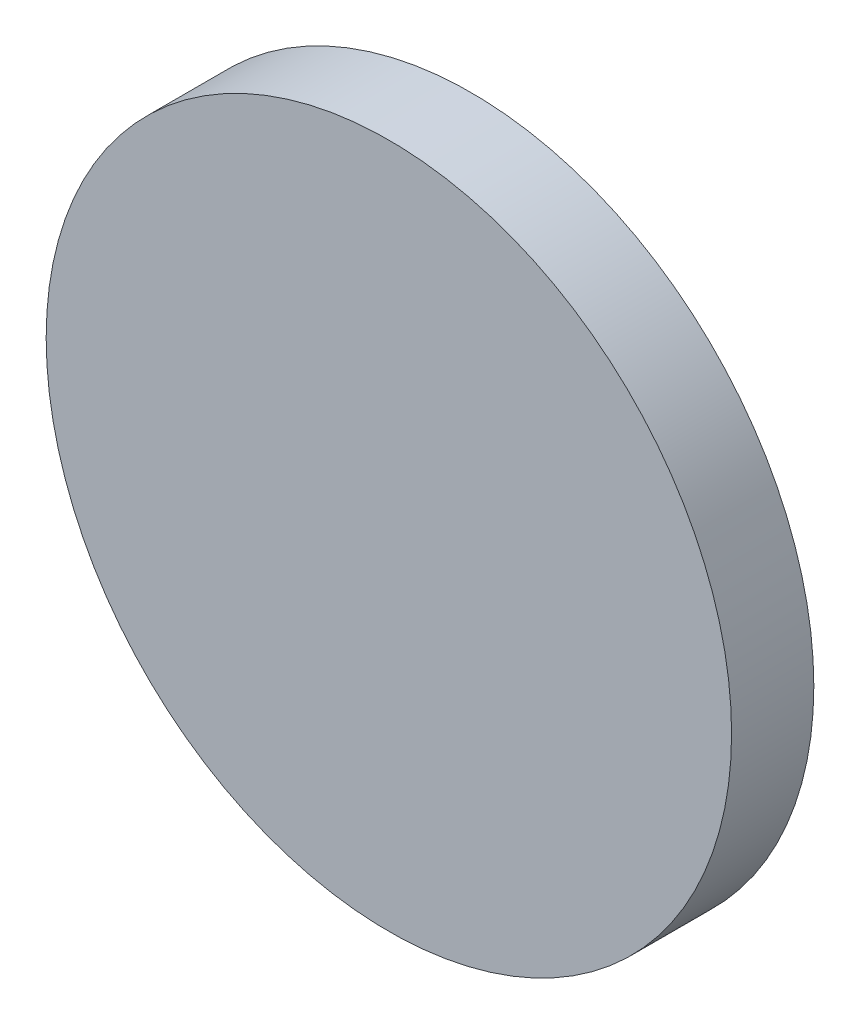
SolidWorks part; units mm, degrees
ref_plane "前视基准面" through (0, 0, 0) normal (0, 0, 1) x (1, 0, 0)
ref_plane "上视基准面" through (0, 0, 0) normal (0, 1, 0) x (1, 0, 0)
ref_plane "右视基准面" through (0, 0, 0) normal (1, 0, 0) x (0, 0, -1)
sketch "草图1" plane through (0, 0, 0) normal (0, 0, 1) x (1, 0, 0)
  circle A0 centre (0, 0) radius 12.5
  dimension "D1" = 25
extrude "凸台-拉伸1" add sketch "草图1" along normal blind 3
